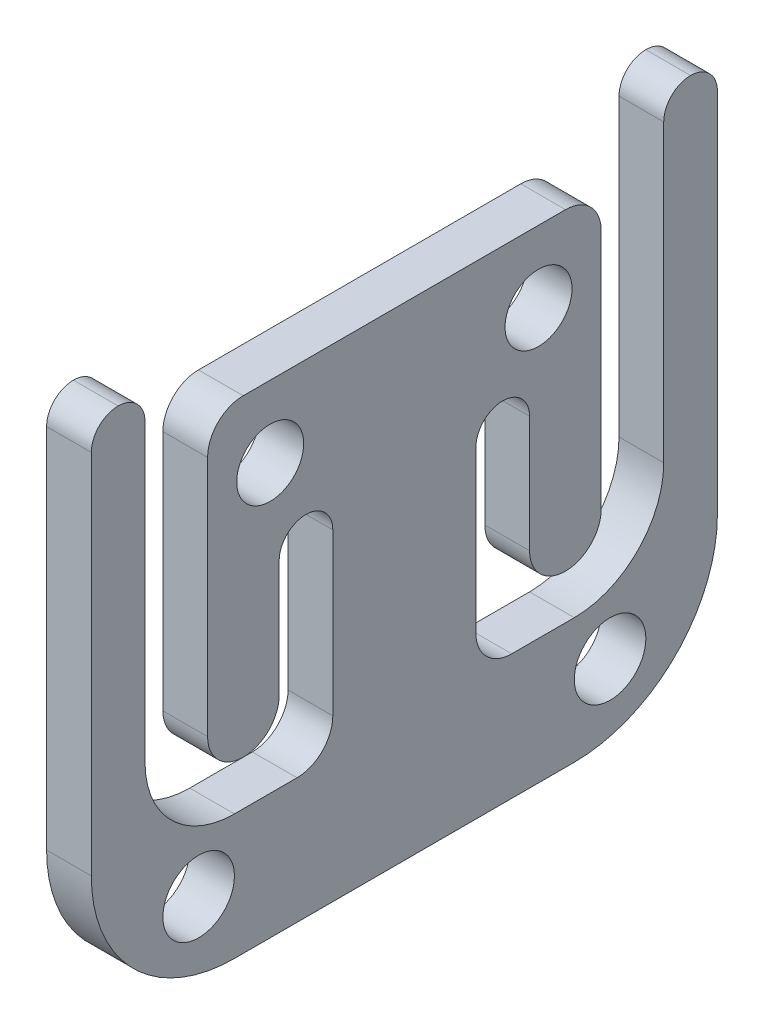
SolidWorks part; units mm, degrees
ref_plane "Front Plane" through (0, 0, 0) normal (0, 0, 1) x (1, 0, 0)
ref_plane "Top Plane" through (0, 0, 0) normal (0, 1, 0) x (1, 0, 0)
ref_plane "Right Plane" through (0, 0, 0) normal (1, 0, 0) x (0, 0, -1)
sketch "Sketch1" plane through (0, 0, 0) normal (1, 0, 0) x (0, 0, -1)
  line L0 (23.5, 7) -> (27, 7)
  line L1 (8, 0) -> (27, 0)
  line L2 (0, 8) -> (0, 28.501)
  line L3 (1.499, 30) -> (1.501, 30)
  line L4 (35, 8) -> (35, 28.501)
  line L5 (0, 8) -> (0, 0) construction
  line L6 (8, 7) -> (11.5, 7)
  line L8 (3, 28.501) -> (3, 12)
  line L9 (33.501, 30) -> (33.499, 30)
  line L10 (32, 28.501) -> (32, 12)
  line L13 (13.5, 9) -> (13.5, 18)
  line L14 (13.5, 27) -> (21.5, 27)
  line L15 (21.5, 9) -> (21.5, 18)
  line L17 (26.51, 27) -> (8.49, 27)
  line L18 (6.5, 25.01) -> (6.5, 11.49)
  line L19 (8.49, 9.5) -> (8.51, 9.5)
  line L20 (10.5, 11.49) -> (10.5, 18)
  line L21 (24.5, 11.49) -> (24.5, 18)
  line L22 (26.51, 9.5) -> (26.49, 9.5)
  line L23 (28.5, 25.01) -> (28.5, 11.49)
  arc A0 (27, 0) -> (35, 8) centre (27, 8) ccw
  arc A1 (8, 0) -> (0, 8) centre (8, 8) cw
  arc A2 (13.5, 18) -> (10.5, 18) centre (12, 18) ccw
  arc A3 (8.51, 9.5) -> (10.5, 11.49) centre (8.51, 11.49) ccw
  arc A4 (6.5, 11.49) -> (8.49, 9.5) centre (8.49, 11.49) ccw
  arc A5 (8.49, 27) -> (6.5, 25.01) centre (8.49, 25.01) ccw
  arc A6 (26.51, 27) -> (28.5, 25.01) centre (26.51, 25.01) cw
  arc A7 (28.5, 11.49) -> (26.51, 9.5) centre (26.51, 11.49) cw
  arc A8 (26.49, 9.5) -> (24.5, 11.49) centre (26.49, 11.49) cw
  arc A9 (21.5, 18) -> (24.5, 18) centre (23, 18) cw
  arc A10 (32, 12) -> (27, 7) centre (27, 12) cw
  arc A11 (3, 12) -> (8, 7) centre (8, 12) ccw
  arc A12 (21.5, 9) -> (23.5, 7) centre (23.5, 9) ccw
  arc A13 (11.5, 7) -> (13.5, 9) centre (11.5, 9) ccw
  arc A14 (33.501, 30) -> (35, 28.501) centre (33.501, 28.501) cw
  arc A15 (33.499, 30) -> (32, 28.501) centre (33.499, 28.501) ccw
  arc A16 (1.501, 30) -> (3, 28.501) centre (1.501, 28.501) cw
  arc A17 (0, 28.501) -> (1.499, 30) centre (1.499, 28.501) cw
  circle A18 centre (10, 23) radius 1.8721
  circle A19 centre (25, 23) radius 1.8721
  circle A20 centre (6, 4) radius 2
  circle A21 centre (29, 4) radius 2
  point P7 (35, 0)
  point P10 (0, 0)
  dimension "D3" = 8
  dimension "D4" = 1.99
  dimension "D5" = 5
  dimension "D6" = 2
  dimension "D7" = 1.499
  dimension "D2" = 35
extrude "Boss-Extrude1" add sketch "Sketch1" along normal blind 2.5 contours A17 L2 A1 L1 A0 L4 A14 L9 A15 L10 A10 L0 A12 L15 A9 L21 A8 L22 A7 L23 A6 L17 L14 A5 L18 A4 L19 A3 L20 A2 L13 A13 L6 A11 L8 A16 L3
